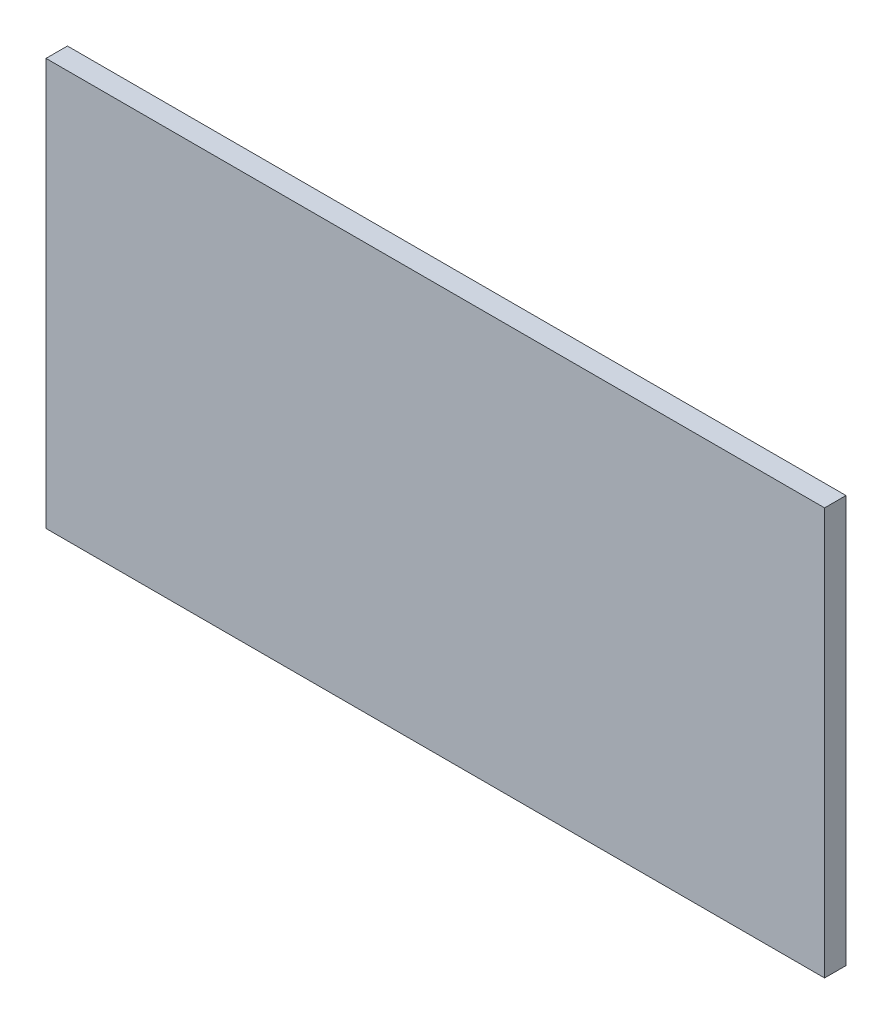
SolidWorks part; units mm, degrees
ref_plane "Front Plane" through (0, 0, 0) normal (0, 0, 1) x (1, 0, 0)
ref_plane "Top Plane" through (0, 0, 0) normal (0, 1, 0) x (1, 0, 0)
ref_plane "Right Plane" through (0, 0, 0) normal (1, 0, 0) x (0, 0, -1)
sketch "Sketch1" plane through (0, 0, 0) normal (0, 0, 1) x (1, 0, 0)
  line L1 (0, 0) -> (-10900, 0)
  line L2 (0, 0) -> (0, 5700)
  line L3 (0, 5700) -> (-10900, 5700)
  line L4 (-10900, 0) -> (-10900, 5700)
  dimension "D1" = 10900
  dimension "D2" = 5700
extrude "Extrude1" add sketch "Sketch1" along normal blind 300
